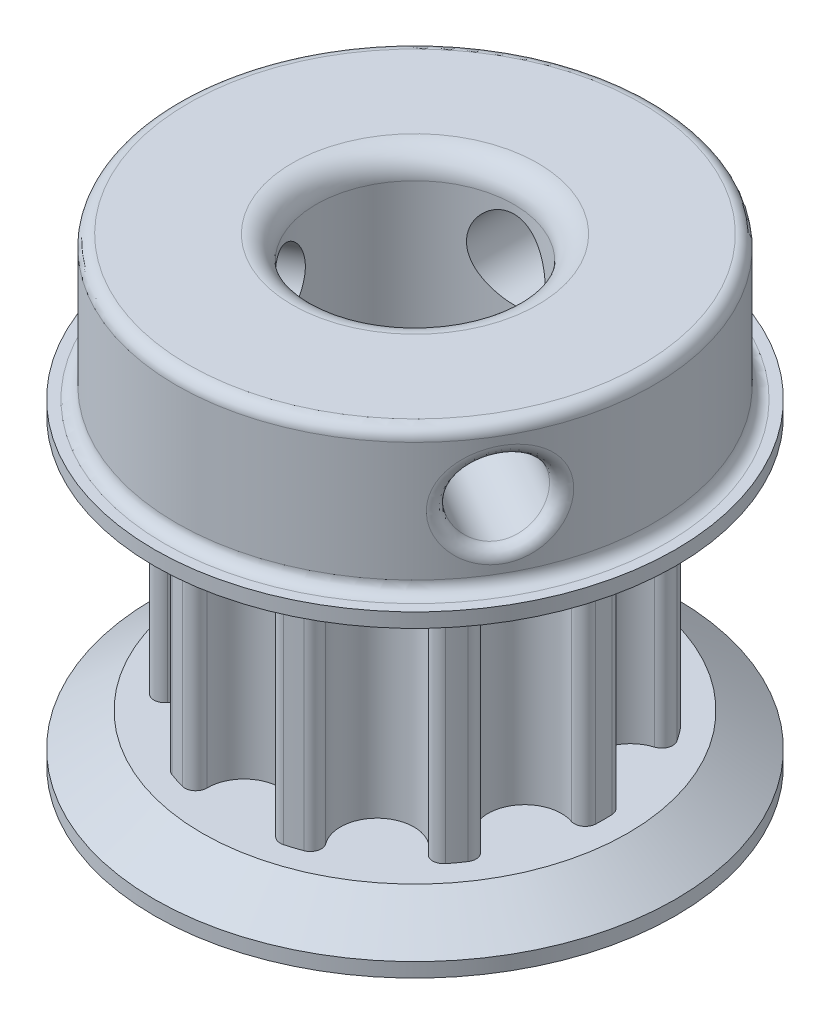
SolidWorks part; units mm, degrees
ref_plane "Plan de face" through (0, 0, 0) normal (0, 0, 1) x (1, 0, 0)
ref_plane "Plan de dessus" through (0, 0, 0) normal (0, 1, 0) x (1, 0, 0)
ref_plane "Plan de droite" through (0, 0, 0) normal (1, 0, 0) x (0, 0, -1)
sketch "Esquisse1" plane through (0, 0, 0) normal (0, 1, 0) x (1, 0, 0)
  line L0 (0, 0) -> (-2.449, 7.5372)
  line L2 (2.449, 7.5372) -> (0, 0)
  line L3 (0, 7.9251) -> (0, 0) construction
  line L4 (-2.449, 7.5372) -> (2.449, 7.5372) construction
  circle A1 centre (0, 0) radius 7.9251 construction
  arc A2 (-1.5429, 7.1881) -> (1.5429, 7.1881) centre (0, 7.1681) ccw
  arc A3 (-2.449, 7.5372) -> (-2.1236, 7.6353) centre (0, 0) cw
  arc A4 (-2.1236, 7.6353) -> (-1.5429, 7.1881) centre (-2.0008, 7.1941) cw
  arc A5 (2.449, 7.5372) -> (2.1236, 7.6353) centre (0, 0) ccw
  arc A6 (2.1236, 7.6353) -> (1.5429, 7.1881) centre (2.0008, 7.1941) ccw
  arc A7 (-1.5429, 7.1881) -> (-1.4081, 7.799) centre (0, 7.1681) cw construction
  arc A8 (1.5429, 7.1881) -> (1.4081, 7.799) centre (0, 7.1681) ccw construction
  point P6 (0, 5.6251)
  dimension "D2" = 1.543
  dimension "D3" = 0.458
  dimension "D1" = 4.898
  dimension "D4" = 2.3
  dimension "D5" = 36
extrude "Boss.-Extru.1" add sketch "Esquisse1" along normal blind 9.3
pattern_circular "Répétition circulaire1" count 10 over 360 about axis through (0, 0, 0) along (0, 1, 0) of "Boss.-Extru.1"
ref_plane "Plan1" through (0, 4.65, 0) normal (0, -1, 0) x (-1, 0, 0)
sketch "Esquisse2" plane through (0, 9.3, 0) normal (0, 1, 0) x (1, 0, 0)
  circle A0 centre (0, 0) radius 10.9251
  arc A1 (-6.2059, 4.9289) -> (-6.6054, 4.3791) centre (0, 0) ccw construction
  dimension "D1" = 3
extrude "Boss.-Extru.2" add sketch "Esquisse2" along normal blind 2
mirror "Symétrie1" about plane through (0, 4.65, 0) normal (0, -1, 0) of "Boss.-Extru.2"
chamfer "Chanfrein1" distance 2 angle 35 2 edges at (0, 9.3, 10.9251) (0, 0, 10.9251)
sketch "Esquisse4" plane through (0, 11.3, 0) normal (0, 1, 0) x (1, 0, 0)
  circle A0 centre (0, 0) radius 10
  dimension "D1" = 20
extrude "Boss.-Extru.3" add sketch "Esquisse4" along normal blind 6
sketch "Esquisse5" plane through (0, 0, 0) normal (0, 0, 1) x (1, 0, 0)
  line L0 (0, 0) -> (0, 14.3) construction
  line L1 (10, 17.3) -> (-10, 17.3) construction
  circle A0 centre (0, 14.3) radius 1.65
  dimension "D2" = 3.3
  dimension "D1" = 3
extrude "Enlèv. mat.-Extru.2" cut sketch "Esquisse5" against normal through all
pattern_circular "Répétition circulaire2" count 3 over 360 about axis through (0, 17.3, 0) along (0, -1, 0) of "Enlèv. mat.-Extru.2"
sketch "Esquisse3" plane through (0, 17.3, 0) normal (0, 1, 0) x (1, 0, 0)
  circle A0 centre (0, 0) radius 4.15
  dimension "D1" = 8.3
extrude "Enlèv. mat.-Extru.1" cut sketch "Esquisse3" against normal up to next
fillet "Congé1" radius 1 2 edges at (0, -2, -4.15) (0, 17.3, 4.15)
fillet "Congé2" radius 0.5 5 edges at (0, 11.3, 10) (0, 17.3, 10) (0.3544, 12.6885, -9.9937) (-7.7413, 13.9455, 6.3302) (9.3528, 13.9455, 3.5391)
equation "\"nb_tooth\"= 10"
equation "\"D5@Esquisse1\"=360/\"nb_tooth\""
equation "\"D1@Répétition circulaire1\"=\"nb_tooth\""
